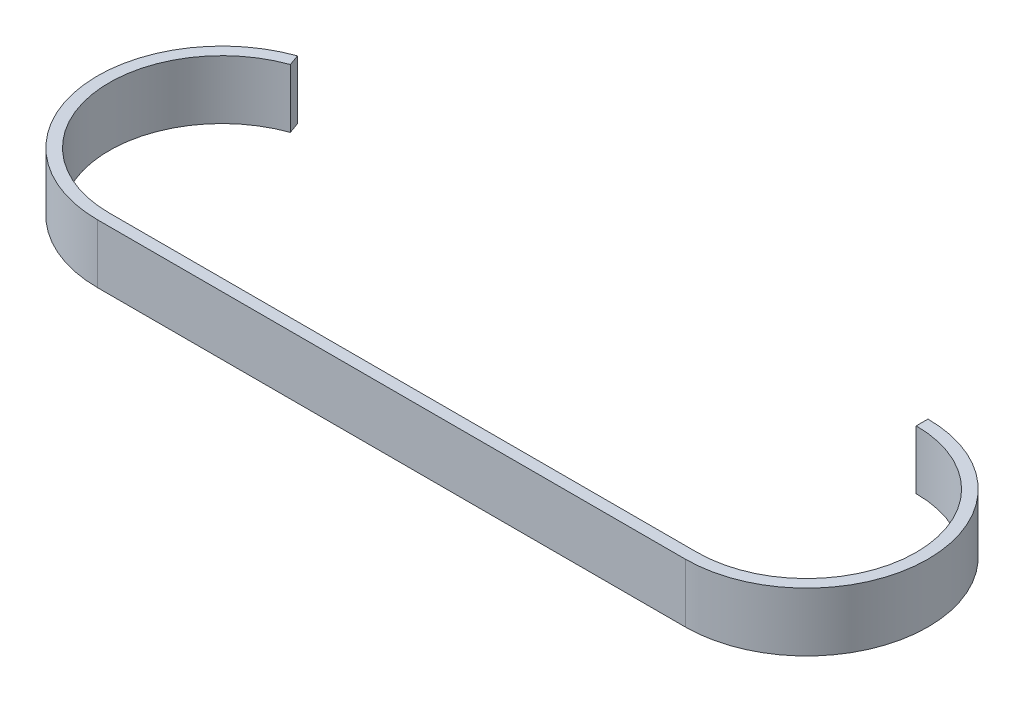
SolidWorks part; units mm, degrees
ref_plane "Front Plane" through (0, 0, 0) normal (0, 0, 1) x (1, 0, 0)
ref_plane "Top Plane" through (0, 0, 0) normal (0, 1, 0) x (1, 0, 0)
ref_plane "Right Plane" through (0, 0, 0) normal (1, 0, 0) x (0, 0, -1)
sketch "Sketch1" plane through (0, 0, 0) normal (0, 1, 0) x (1, 0, 0)
  line L0 (0, 0) -> (127, 0)
  arc A0 (0, 0) -> (-8.2016, 47.3355) centre (0, 24.3783) cw
  arc A1 (127, 0) -> (127, 47.3355) centre (127, 23.6678) ccw
  dimension "D1" = 23.6678
  dimension "D3" = 24.3783
  dimension "D2" = 127
extrude "Extrude-Thin1" add sketch "Sketch1" along normal blind 12.7 thin
